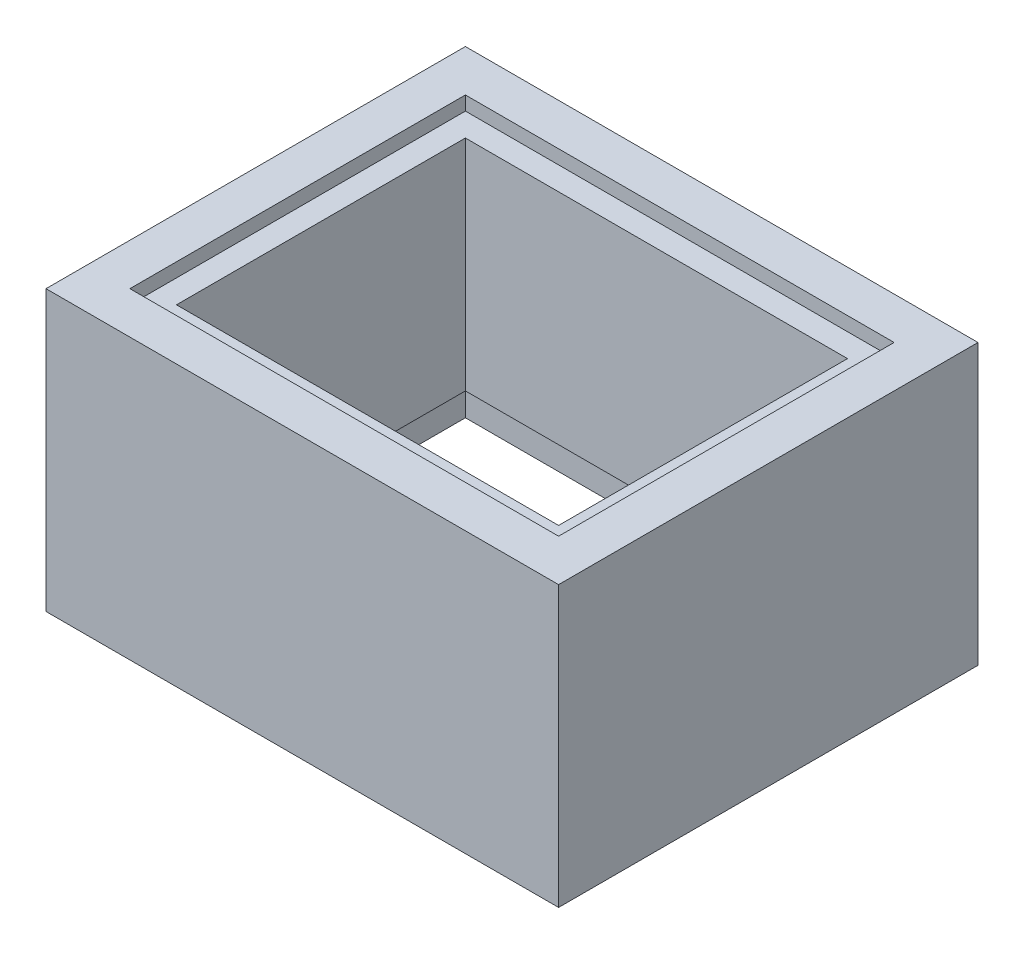
SolidWorks part; units mm, degrees
ref_plane "Front Plane" through (0, 0, 0) normal (0, 0, 1) x (1, 0, 0)
ref_plane "Top Plane" through (0, 0, 0) normal (0, 1, 0) x (1, 0, 0)
ref_plane "Right Plane" through (0, 0, 0) normal (1, 0, 0) x (0, 0, -1)
sketch "Sketch2" plane through (0, 0, 0) normal (0, 1, 0) x (1, 0, 0)
  line L1 (0, 0) -> (110, 0)
  line L2 (0, 0) -> (0, 90)
  line L3 (0, 90) -> (110, 90)
  line L4 (110, 0) -> (110, 90)
  dimension "D1" = 110
  dimension "D2" = 90
extrude "Boss-Extrude2" add sketch "Sketch2" along normal blind 60
sketch "Sketch5" plane through (0, 60, 0) normal (0, 1, 0) x (1, 0, 0)
  line L14 (101, 9) -> (101, 81)
  line L15 (9, 9) -> (101, 9)
  line L16 (101, 81) -> (9, 81)
  line L17 (9, 81) -> (9, 9)
  line L18 (101, 9) -> (101, 81)
  line L19 (9, 9) -> (101, 9)
  line L20 (101, 81) -> (9, 81)
  line L21 (9, 81) -> (9, 9)
  dimension "D1" = 9
extrude "Cut-Extrude3" cut sketch "Sketch5" against normal blind 3
sketch "Sketch6" plane through (0, 0, 0) normal (0, -1, 0) x (1, 0, 0)
  line L14 (9, -81) -> (101, -81)
  line L15 (101, -81) -> (101, -9)
  line L16 (9, -9) -> (9, -81)
  line L17 (101, -9) -> (9, -9)
  line L18 (9, -81) -> (101, -81)
  line L19 (101, -81) -> (101, -9)
  line L20 (9, -9) -> (9, -81)
  line L21 (101, -9) -> (9, -9)
  dimension "D1" = 9
extrude "Cut-Extrude4" cut sketch "Sketch6" against normal blind 10
sketch "Sketch7" plane through (0, 57, 0) normal (0, 1, 0) x (1, 0, 0)
  line L8 (14, 14) -> (96, 14)
  line L9 (96, 14) -> (96, 76)
  line L10 (96, 76) -> (14, 76)
  line L11 (14, 76) -> (14, 14)
  line L12 (14, 14) -> (96, 14)
  line L13 (96, 14) -> (96, 76)
  line L14 (96, 76) -> (14, 76)
  line L15 (14, 76) -> (14, 14)
  dimension "D1" = 5
extrude "Cut-Extrude5" cut sketch "Sketch7" against normal blind 60
